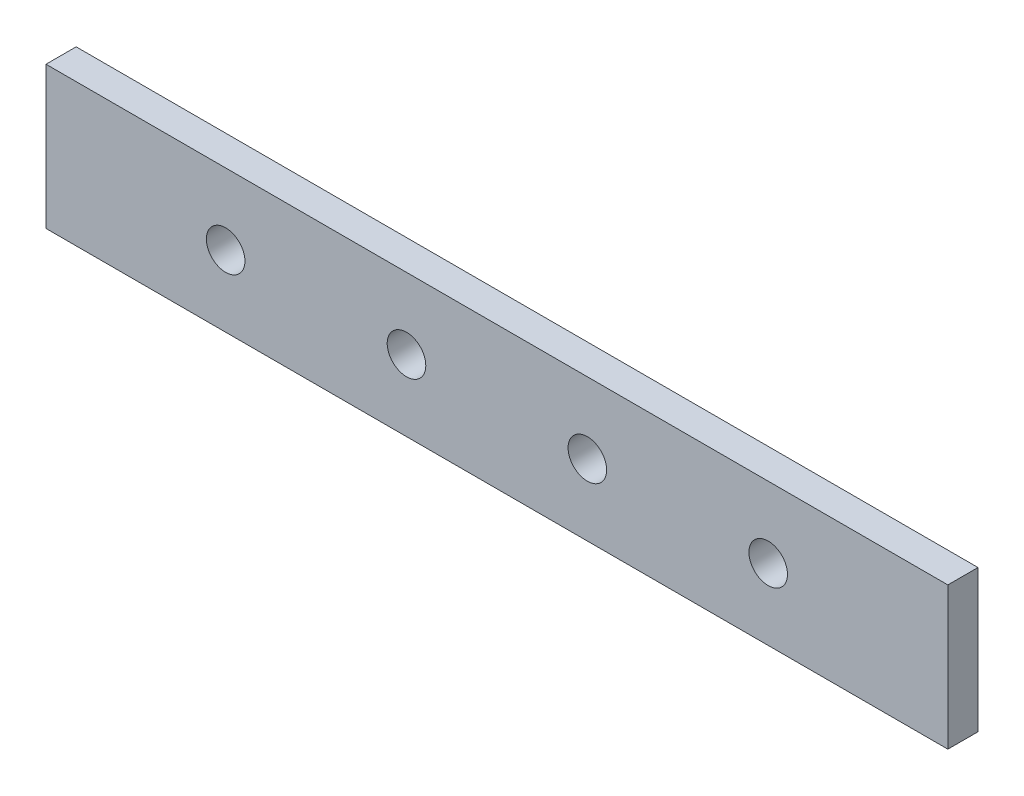
SolidWorks part; units mm, degrees
ref_plane "Alzado" through (0, 0, 0) normal (0, 0, 1) x (1, 0, 0)
ref_plane "Planta" through (0, 0, 0) normal (0, 1, 0) x (1, 0, 0)
ref_plane "Vista lateral" through (0, 0, 0) normal (1, 0, 0) x (0, 0, -1)
sketch "Croquis1" plane through (0, 0, 0) normal (0, 0, 1) x (1, 0, 0)
  line L0 (37.4, -81.9) -> (37.4, -70.1)
  line L1 (37.4, -70.1) -> (-37.4, -70.1)
  line L2 (-37.4, -70.1) -> (-37.4, -81.9)
  line L3 (-37.4, -81.9) -> (37.4, -81.9)
  line L4 (37.5, -82) -> (37.5, -70)
  line L5 (37.5, -70) -> (-37.5, -70)
  line L6 (37.5, -82) -> (37.5, -70)
  line L7 (-37.5, -82) -> (37.5, -82)
  line L9 (37.5, -70) -> (-37.5, -70)
  line L11 (-37.5, -82) -> (37.5, -82)
  line L84 (37.5, -82) -> (37.5, -70) construction
  line L85 (-37.5, -70) -> (-37.5, -82) construction
  line L86 (-37.5, -70) -> (-37.5, -82)
  line L87 (-37.5, -70) -> (-37.5, -82)
  dimension "D1" = 0
  dimension "D2" = 0.1
extrude "Saliente-Extruir1" add sketch "Croquis1" along normal blind 2.5
sketch "Croquis2" plane through (0, 0, 2.5) normal (0, 0, 1) x (1, 0, 0)
  circle A0 centre (-22.5, -76) radius 1.6 construction
  circle A1 centre (22.5, -76) radius 1.6 construction
  circle A2 centre (-7.5, -76) radius 1.6 construction
  circle A3 centre (7.5, -76) radius 1.6 construction
  circle A4 centre (-22.5, -76) radius 1.6
  circle A5 centre (22.5, -76) radius 1.6
  circle A6 centre (-7.5, -76) radius 1.6
  circle A7 centre (7.5, -76) radius 1.6
extrude "Cortar-Extruir1" cut sketch "Croquis2" against normal up to next
